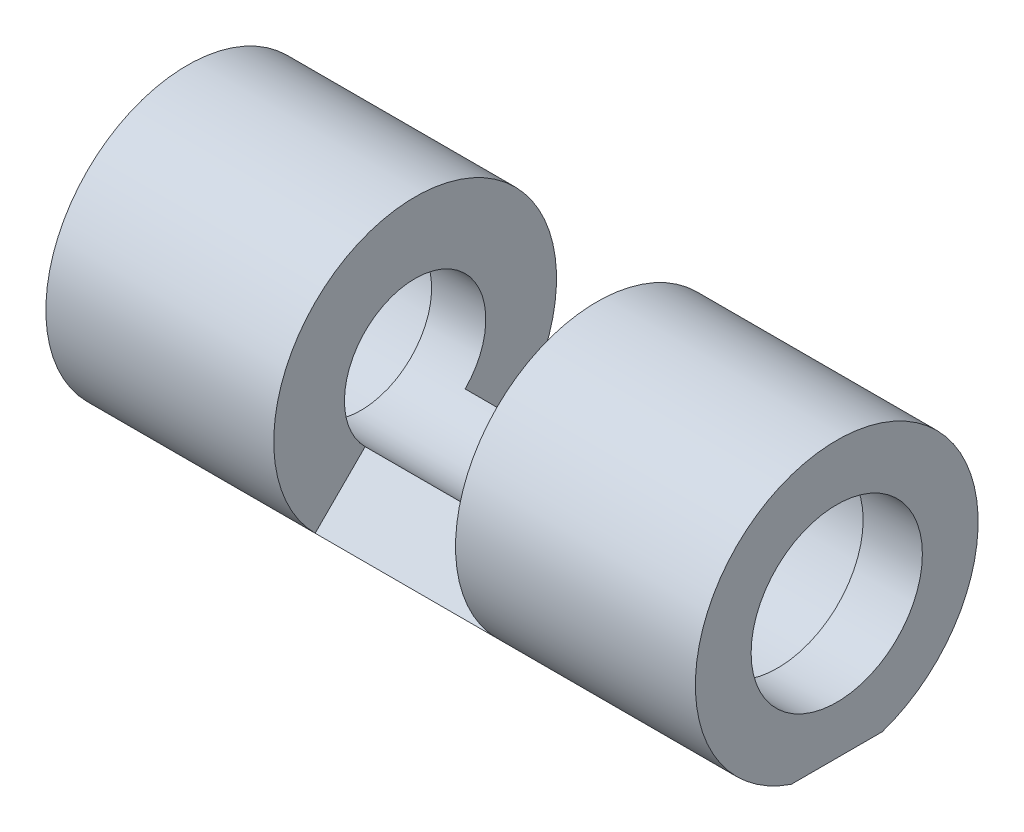
SolidWorks part; units mm, degrees
ref_plane "Front Plane" through (0, 0, 0) normal (0, 0, 1) x (1, 0, 0)
ref_plane "Top Plane" through (0, 0, 0) normal (0, 1, 0) x (1, 0, 0)
ref_plane "Right Plane" through (0, 0, 0) normal (1, 0, 0) x (0, 0, -1)
sketch "Sketch1" plane through (0, 0, 0) normal (0, 0, 1) x (1, 0, 0)
  line L0 (-29.384, 0) -> (35.5601, 0) construction
  line L3 (-21.3682, 15) -> (-21.3682, 10)
  line L10 (-21.3682, 15) -> (-37.5601, 15)
  line L11 (-37.5601, 15) -> (-37.5601, 10)
  line L12 (45.9369, 20) -> (-45.9369, 20)
  line L13 (-45.9369, 20) -> (-45.9369, 10)
  line L14 (-45.9369, 10) -> (-37.5601, 10)
  line L15 (0, 41.1452) -> (0, -36.1722) construction
  line L28 (-21.3682, 10) -> (21.3682, 10)
  line L29 (45.9369, 10) -> (37.5601, 10)
  line L30 (45.9369, 20) -> (45.9369, 10)
  line L31 (37.5601, 15) -> (37.5601, 10)
  line L32 (21.3682, 15) -> (37.5601, 15)
  line L33 (21.3682, 15) -> (21.3682, 10)
  point P8 (0, 10)
  point P10 (0, 10)
  point P17 (0, 20)
  point P19 (0, 20)
revolve "Revolve1" add sketch "Sketch1" angle 360 about L0
sketch "Sketch2" plane through (0, 0, 0) normal (0, 0, 1) x (1, 0, 0)
  line L0 (-13.7019, 25.7881) -> (-13.7019, 8.8526)
  line L1 (-13.7019, 8.8526) -> (12.0092, 8.8526)
  line L2 (12.0092, 8.8526) -> (12.0092, 25.7881)
  line L3 (12.0092, 25.7881) -> (-13.7019, 25.7881)
  line L4 (-31.7357, 0) -> (28.6156, 0) construction
revolve "Cut-Revolve1" cut sketch "Sketch2" angle 270 mid plane about L4
sketch "Sketch3" plane through (-45.9369, 0, 0) normal (-1, 0, 0) x (0, 0, 1)
  circle A0 centre (0, 0) radius 12.1123
extrude "Cut-Extrude1" cut sketch "Sketch3" against normal blind 12
mirror "Mirror1" about plane through (0, 0, 0) normal (1, 0, 0) of "Cut-Extrude1"
sketch "Sketch4" plane through (0, 0, 0) normal (1, 0, 0) x (0, 0, -1)
  line L0 (0, 0) -> (0, -34.0213) construction
  line L1 (-23.2786, -18.9369) -> (32.5161, -18.9369)
  line L2 (32.5161, -18.9369) -> (-2.217, -46.4648)
  line L3 (-2.217, -46.4648) -> (-23.2786, -18.9369)
extrude "Cut-Extrude2" cut sketch "Sketch4" against normal through all both and the other way through all
